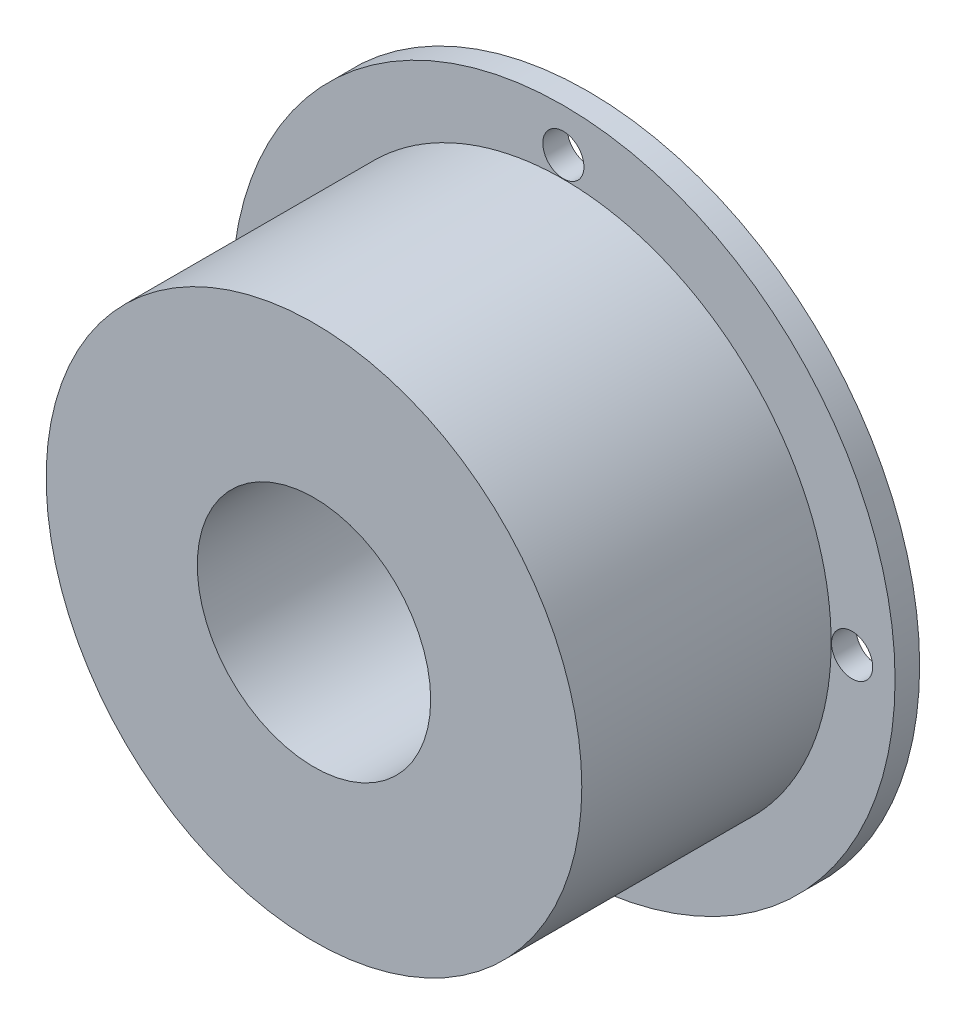
SolidWorks part; units mm, degrees
ref_plane "前基準面" through (0, 0, 0) normal (0, 0, 1) x (1, 0, 0)
ref_plane "上基準面" through (0, 0, 0) normal (0, 1, 0) x (1, 0, 0)
ref_plane "右基準面" through (0, 0, 0) normal (1, 0, 0) x (0, 0, -1)
sketch "草圖1" plane through (0, 0, 0) normal (0, 0, 1) x (1, 0, 0)
  circle A0 centre (0, 0) radius 9.5
  circle A1 centre (0, 0) radius 21.8
  dimension "D1" = 19
  dimension "D2" = 43.6
extrude "填料-伸長1" add sketch "草圖1" along normal blind 22.3
sketch "草圖2" plane through (0, 0, 0) normal (0, 0, -1) x (-1, 0, 0)
  line L0 (-27, 0) -> (27, 0) construction
  line L1 (0, 27) -> (0, -27) construction
  circle A0 centre (0, 0) radius 27
  circle A1 centre (0, 0) radius 21.8
  circle A2 centre (0, 23.5) radius 1.675
  circle A3 centre (0, -23.5) radius 1.675
  circle A4 centre (23.5, 0) radius 1.675
  circle A5 centre (-23.5, 0) radius 1.675
  circle A6 centre (0, 0) radius 21.8 construction
  dimension "D1" = 54
  dimension "D6" = 3.35
  dimension "D2" = 47
  dimension "D3" = 47
  dimension "D4" = 23.5
  dimension "D5" = 23.5
extrude "填料-伸長2" add sketch "草圖2" against normal blind 2 separate body
